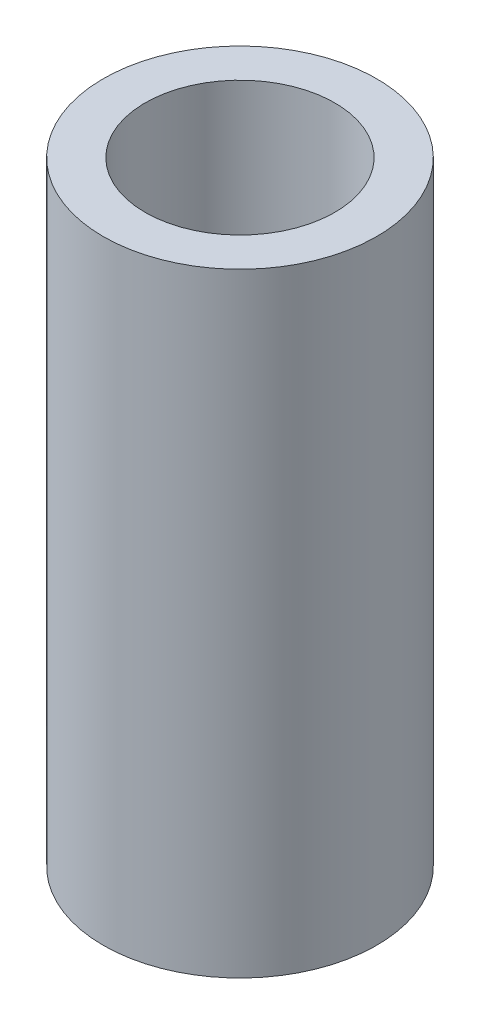
SolidWorks part; units mm, degrees
ref_plane "Front Plane" through (0, 0, 0) normal (0, 0, 1) x (1, 0, 0)
ref_plane "Top Plane" through (0, 0, 0) normal (0, 1, 0) x (1, 0, 0)
ref_plane "Right Plane" through (0, 0, 0) normal (1, 0, 0) x (0, 0, -1)
sketch "Sketch1" plane through (0, 0, 0) normal (0, 1, 0) x (1, 0, 0)
  circle A0 centre (0, 0) radius 1.7
  circle A1 centre (0, 0) radius 2.45
  dimension "D1" = 3.4
  dimension "D2" = 4.9
extrude "Boss-Extrude1" add sketch "Sketch1" along normal blind 11
